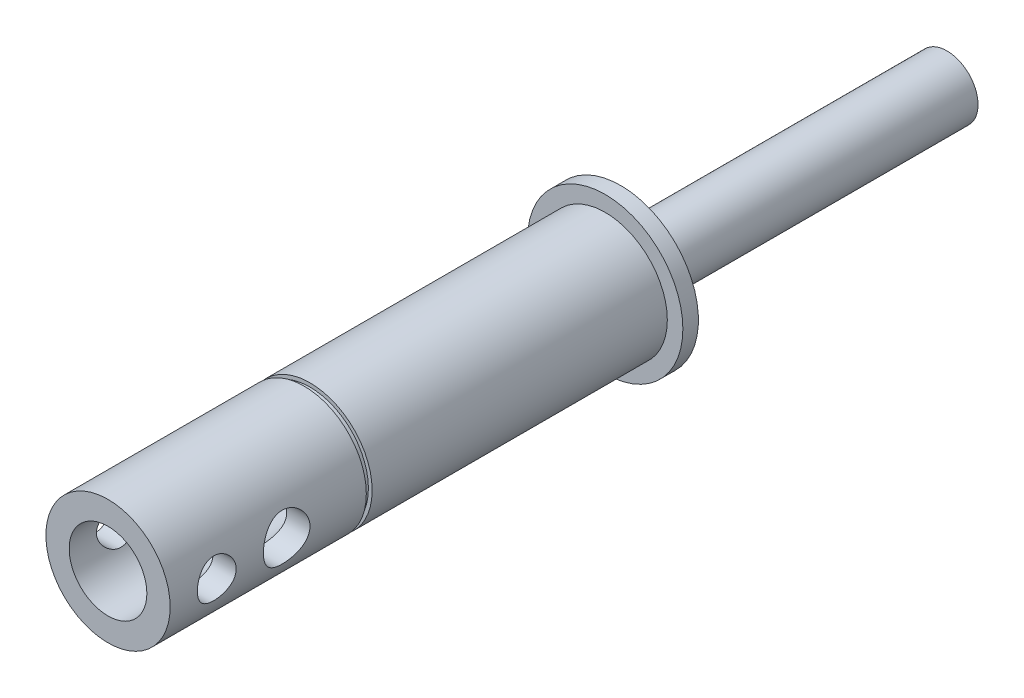
SolidWorks part; units mm, degrees
other "Markup1"
sketch "Sketch20" plane through (-15.875, -15.875, 171.45) normal (-1, 0, 0) x (0, 0, -1)
material "6061 Alloy"
ref_plane "Front Plane" through (0, 0, 0) normal (0, 0, 1) x (1, 0, 0)
ref_plane "Top Plane" through (0, 0, 0) normal (0, 1, 0) x (1, 0, 0)
ref_plane "Right Plane" through (0, 0, 0) normal (1, 0, 0) x (0, 0, -1)
sketch "Sketch1" plane through (0, 0, 0) normal (0, 0, 1) x (1, 0, 0)
  circle A0 centre (0, 0) radius 15.875
  dimension "D1" = 31.75
extrude "RawStock" add sketch "Sketch1" along normal blind 194.6402
sketch "Sketch10" plane through (0, 0, 194.6402) normal (0, 0, 1) x (1, 0, 0)
  circle A0 centre (0, 0) radius 12.7
extrude "FacingOp" cut sketch "Sketch10" against normal blind 23.1902
hole_wizard "ReliefHole" positions "Sketch2" profile "Sketch3" legacy
sketch "Sketch2" plane through (0, 0, 194.6402) normal (0, 0, 1) x (1, 0, 0)
  point P0 (0, 0)
sketch "Sketch3" plane through (0, 0, 194.6402) normal (1, 0, 0) x (0, -1, 0)
  line L0 (0, 0) -> (0, 95.8905)
  line L1 (0, 95.8905) -> (6.35, 92.075)
  line L2 (6.35, 92.075) -> (6.35, 0)
  line L4 (6.35, 0) -> (0, 0)
  line L6 (0, 95.8905) -> (-6.35, 92.075) construction
  line L7 (0, -4.2442) -> (0, 117.3081) construction
  dimension "Diameter" = 12.7
  dimension "Depth" = 92.075
  dimension "Drill Angle" = 118
hole_wizard "WiresHole" positions "Sketch4" profile "Sketch5" legacy
sketch "Sketch4" plane through (0, 0, 194.6402) normal (0, 0, 1) x (1, 0, 0)
  point P0 (0, 0)
sketch "Sketch5" plane through (0, 0, 194.6402) normal (1, 0, 0) x (0, -1, 0)
  line L0 (0, 0) -> (0, 120.0345)
  line L1 (0, 120.0345) -> (7.9375, 115.2652)
  line L2 (7.9375, 115.2652) -> (7.9375, 0)
  line L4 (7.9375, 0) -> (0, 0)
  line L6 (0, 120.0345) -> (-7.9375, 115.2652) construction
  line L7 (0, -4.2442) -> (0, 117.3081) construction
  dimension "Diameter" = 15.875
  dimension "Depth" = 115.2652
  dimension "Drill Angle" = 118
sketch "Sketch6" plane through (0, 0, 194.6402) normal (0, 0, 1) x (1, 0, 0)
  circle A0 centre (0, 0) radius 12.7
  dimension "D1" = 25.4
extrude "ShaftDiam" cut sketch "Sketch6" against normal blind 124.7902 flip side to cut
ref_plane "GroovePlane" through (0, 0, 130.175) normal (0, 0, 1) x (1, 0, 0)
sketch "Sketch7" plane through (0, 0, 130.175) normal (0, 0, 1) x (1, 0, 0)
  circle A0 centre (0, 0) radius 11.938
  dimension "D1" = 23.876
extrude "Groove" cut sketch "Sketch7" along normal blind 1.1906 flip side to cut
sketch "Sketch8" plane through (0, 0, 0) normal (0, 0, -1) x (-1, 0, 0)
  circle A0 centre (0, 0) radius 6.35
  dimension "D1" = 12.7
extrude "EncoderShaft" cut sketch "Sketch8" against normal blind 66.675 flip side to cut
ref_plane "Plane2" through (-12.7, 0, 0) normal (-1, 0, 0) x (0, 1, 0)
sketch "Sketch12" plane through (-12.7, 0, 0) normal (-1, 0, 0) x (0, 1, 0)
  line L0 (-12.7, -171.45) -> (12.7, -171.45) construction
  line L1 (0, -194.6402) -> (0, -74.6057) construction
  line L2 (-7.9375, -171.45) -> (7.9375, -171.45) construction
  circle A0 centre (0, -161.925) radius 3.9687
  circle A1 centre (0, -147.6375) radius 4.7625
  dimension "D1" = 7.9375
  dimension "D3" = 9.525
  dimension "D2" = 9.525
  dimension "D4" = 23.8125
extrude "Holes_Top" cut sketch "Sketch12" against normal through all
ref_plane "Plane1" through (0, -11.938, 0) normal (0, -1, 0) x (-1, 0, 0)
hole_wizard "SlipRingHole" positions "Sketch18" profile "Sketch19" legacy
sketch "Sketch18" plane through (0, 0, 66.675) normal (0, 0, -1) x (-1, 0, 0)
  line L0 (0, 17.4625) -> (0, -17.4625) construction
  circle A0 centre (0, 0) radius 8.7312 construction
  point P0 (0, -8.7312)
  dimension "D1" = 17.4625
sketch "Sketch19" plane through (0, -8.7312, 66.675) normal (1, 0, 0) x (0, 1, 0)
  line L0 (0, 0) -> (0, 26.8308)
  line L1 (0, 26.8308) -> (2.3812, 25.4)
  line L2 (2.3812, 25.4) -> (2.3812, 0)
  line L4 (2.3812, 0) -> (0, 0)
  line L6 (0, 26.8308) -> (-2.3812, 25.4) construction
  line L7 (0, -4.2442) -> (0, 117.3081) construction
  dimension "Diameter" = 4.7625
  dimension "Depth" = 25.4
  dimension "Drill Angle" = 118
